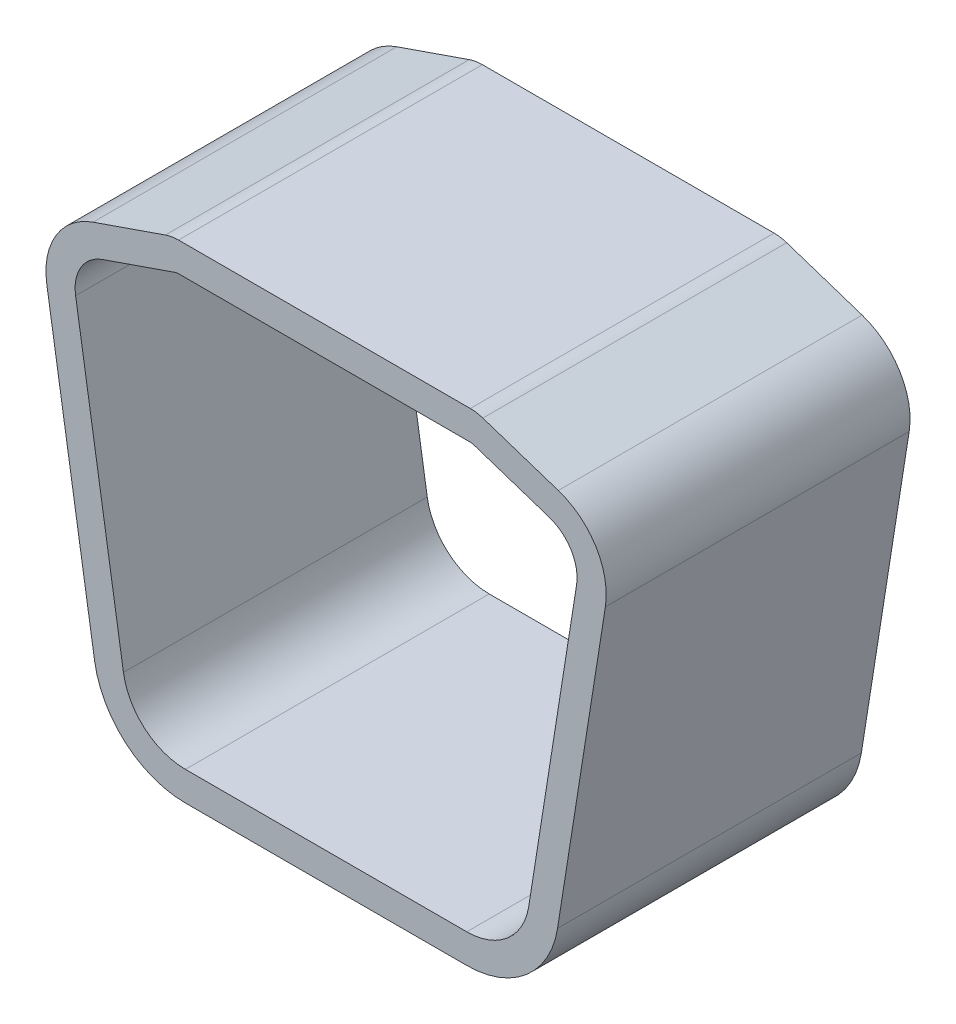
SolidWorks part; units mm, degrees
ref_plane "前视基准面" through (0, 0, 0) normal (0, 0, 1) x (1, 0, 0)
ref_plane "上视基准面" through (0, 0, 0) normal (0, 1, 0) x (1, 0, 0)
ref_plane "右视基准面" through (0, 0, 0) normal (1, 0, 0) x (0, 0, -1)
other "Configuration Table"
sketch "草图1" plane through (0, 0, 0) normal (0, 0, 1) x (1, 0, 0)
  line L0 (12.5339, 23.8842) -> (19.3853, 21.6176)
  line L1 (21.8778, 17.5267) -> (17.5332, -9.9373)
  line L2 (-14.2802, 23.9348) -> (12.2198, 23.9348)
  line L3 (-23.6314, 17.5267) -> (-19.2868, -9.9373)
  line L4 (-21.1875, 21.6011) -> (-14.6074, 23.8797)
  line L5 (-13.6568, -14.7467) -> (11.9032, -14.7467)
  line L6 (13.3662, 26.4001) -> (20.2176, 24.1335)
  line L7 (24.4952, 17.1126) -> (20.1506, -10.3514)
  line L8 (-13.6568, -17.3967) -> (11.9032, -17.3967)
  line L9 (-26.2488, 17.1126) -> (-21.9042, -10.3514)
  line L10 (-22.0547, 24.1052) -> (-15.4746, 26.3838)
  line L11 (-14.2802, 26.5848) -> (12.2198, 26.5848)
  arc A0 (21.8778, 17.5267) -> (19.3853, 21.6176) centre (18.2232, 18.1048) ccw
  arc A1 (12.5339, 23.8842) -> (12.2198, 23.9348) centre (12.2198, 22.9348) ccw
  arc A2 (11.9032, -14.7467) -> (17.5332, -9.9373) centre (11.9032, -9.0467) ccw
  arc A3 (-19.2868, -9.9373) -> (-13.6568, -14.7467) centre (-13.6568, -9.0467) ccw
  arc A4 (-21.1875, 21.6011) -> (-23.6314, 17.5267) centre (-19.9768, 18.1048) ccw
  arc A5 (-14.2802, 23.9348) -> (-14.6074, 23.8797) centre (-14.2802, 22.9348) ccw
  arc A6 (24.4952, 17.1126) -> (20.2176, 24.1335) centre (18.2232, 18.1048) ccw
  arc A7 (11.9032, -17.3967) -> (20.1506, -10.3514) centre (11.9032, -9.0467) ccw
  arc A8 (-21.9042, -10.3514) -> (-13.6568, -17.3967) centre (-13.6568, -9.0467) ccw
  arc A9 (-22.0547, 24.1052) -> (-26.2488, 17.1126) centre (-19.9768, 18.1048) ccw
  arc A10 (-14.2802, 26.5848) -> (-15.4746, 26.3838) centre (-14.2802, 22.9348) ccw
  arc A11 (13.3662, 26.4001) -> (12.2198, 26.5848) centre (12.2198, 22.9348) ccw
  dimension "D1" = 7.4
  dimension "D2" = 11.4
  dimension "D3" = 2.65
extrude "凸台-拉伸1" add sketch "草图1" along normal blind 27.6
